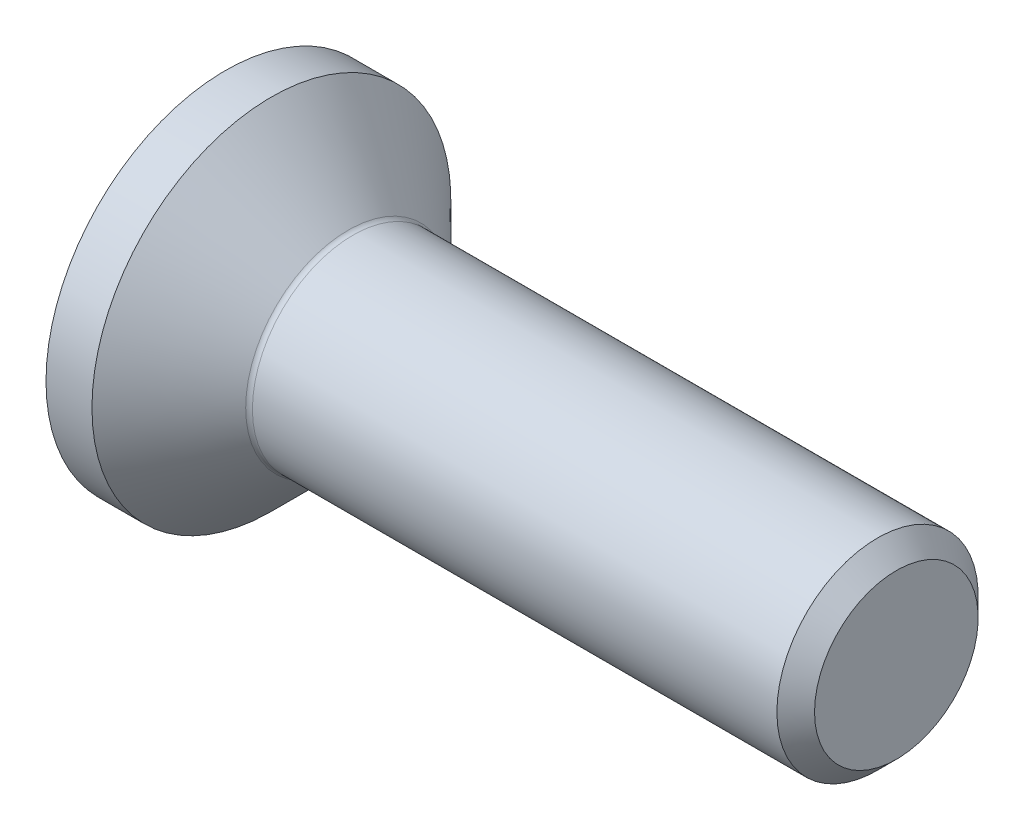
SolidWorks part; units mm, degrees
ref_plane "Plane1" through (0, 0, 0) normal (0, 0, 1) x (1, 0, 0)
ref_plane "Plane2" through (0, 0, 0) normal (0, 1, 0) x (1, 0, 0)
ref_plane "Plane3" through (0, 0, 0) normal (1, 0, 0) x (0, 0, -1)
sketch "BodySke" plane through (0, 0, 0) normal (0, 0, 1) x (1, 0, 0)
  line L0 (0, 0) -> (0, 2.675)
  line L1 (0.685, 2.675) -> (1.86, 1.5)
  line L2 (0, 2.675) -> (0.685, 2.675)
  line L3 (1.86, 1.5) -> (9.7195, 1.5)
  line L4 (10, 1.2195) -> (10, 0)
  line L5 (10, 0) -> (0, 0)
  line L6 (0, 0) -> (127, 0) construction
  line L7 (0.685, -2.675) -> (1.86, -1.5) construction
  line L8 (10, 1.2195) -> (9.7195, 1.5)
  line L9 (0, -2.675) -> (0.685, -2.675) construction
  line L10 (10, -1.2195) -> (9.7195, -1.5) construction
  line L11 (2.36, 7.85) -> (2.36, -14.375) construction
  line L12 (0, 19.05) -> (0, -3.175) construction
  dimension "D1" = 0.685
  dimension "Diameter" = 3
  dimension "Head_ht" = 1.86
  dimension "Length" = 10
  dimension "Body_ch_ang" = 45
  dimension "Head_dia" = 5.35
  dimension "Minor_dia" = 2.439
  dimension "Head_ang" = 90
  dimension "Advance" = 0.5
  dimension "Thread_nom" = 10
revolve "BaseBody" add sketch "BodySke" angle 360 about L6
cosmetic thread "ThreadCosmetic" [suppressed] parameters "Thread_length"=7.14, "Thread_minor"=2.439
fillet "Fillet1" radius 0.1 1 edges at (1.86, 0, 1.5)
sketch "Sketch2" plane through (0, 0, 0) normal (0, 0, 1) x (1, 0, 0)
  line L0 (0, 1) -> (1.1, 1)
  line L1 (1.1, 1) -> (1.6774, 0)
  line L2 (0, 0) -> (127, 0) construction
  line L3 (1.6774, 0) -> (0, 0)
  line L4 (0, 0) -> (0, 1)
  line L5 (0, -1) -> (1.1, -1) construction
  line L6 (0, 0) -> (47.625, 0) construction
  line L8 (0, 2.675) -> (0, -2.675) construction
  dimension "D2" = 60
  dimension "PreBroach_depth" = 1.1
  dimension "PreBroach_dia" = 2
revolve "PreBroach" cut sketch "Sketch2" angle 360 about L6
sketch "Sketch3" plane through (0, 0, 0) normal (-1, 0, 0) x (0, 0, 1)
  line L0 (-1, -0.5774) -> (-1, 0.5774)
  line L1 (-1, 0.5774) -> (0, 1.1547)
  line L2 (0, 1.1547) -> (1, 0.5774)
  line L3 (1, 0.5774) -> (1, -0.5774)
  line L4 (1, -0.5774) -> (0, -1.1547)
  line L5 (0, -1.1547) -> (-1, -0.5774)
  dimension "D1" = 1
  dimension "D2" = 1
  dimension "D3" = 2
  dimension "Hex_size" = 2
extrude "Hex" cut sketch "Sketch3" against normal blind 1.1
sketch "ThdSchSke" plane through (0, 0, 0) normal (0, 0, 1) x (1, 0, 0)
  line L0 (2.86, -1.2195) -> (2.6636, -1.5)
  line L1 (2.86, -1.2195) -> (3.0564, -1.5)
  line L2 (3.0564, -1.5) -> (3.0564, -1.875)
  line L3 (-3.175, 0) -> (5.1513, 0) construction
  line L4 (0, 2.675) -> (0, -2.675) construction
  line L5 (3.0564, -1.875) -> (2.6636, -1.875)
  line L6 (2.6636, -1.875) -> (2.6636, -1.5)
  dimension "Thread_minor" = 2.439
  dimension "Diameter" = 3
  dimension "Start" = 2.86
  dimension "SideAngle" = 55
  dimension "VeeAngle" = 70
  dimension "Overcut" = 3.75
revolve "ThreadSchematic" [suppressed] cut sketch "ThdSchSke" angle 360 about L3
pattern_linear "ThdSchPat" [suppressed]
equation "\"Thread_minor@ThreadCosmetic\"  =  \"Minor_dia@BodySke\""
equation "\"D1@Sketch3\" = \"Hex_size@Sketch3\" / 2"
equation "\"D2@Sketch3\" = \"D1@Sketch3\""
equation "\"D3@Sketch3\" = \"Hex_size@Sketch3\""
equation "\"Thread_length@ThreadCosmetic\" = ((sgn( (\"Length@BodySke\" - \"Advance@BodySke\" * 2.0 - \"Head_ht@BodySke\" ) - \"Thread_nom@BodySke\" )-1)*( (\"Length@BodySke\" - \"Advance@BodySke\" * 2.0 - \"Head_ht@BodySke\" ) - \"Thread_nom@BodySke\" ))/-2+ \"Thread_nom@BodySke\""
equation "\"Thread_minor@ThdSchSke\" = \"Minor_dia@BodySke\""
equation "\"Diameter@ThdSchSke\" = \"Diameter@BodySke\""
equation "\"Overcut@ThdSchSke\" = \"Diameter@BodySke\" * 1.25"
equation "\"Start@ThdSchSke\" = 0.000001 + \"Length@BodySke\" - \"Thread_length@ThreadCosmetic\"  '---Countersunk---"
equation "\"Num_threads@ThdSchPat\" = int( \"Thread_length@ThreadCosmetic\" / \"Advance@BodySke\" + 0.999 )  + 1"
equation "\"Advance@ThdSchPat\" = \"Thread_length@ThreadCosmetic\" /  (\"Num_threads@ThdSchPat\" - 1) 'relax it"
equation "\"Num_threads@ThdSchPat\" = \"Num_threads@ThdSchPat\" - sgn( \"Num_threads@ThdSchPat\" - 1) '---chamfered tips only---"
